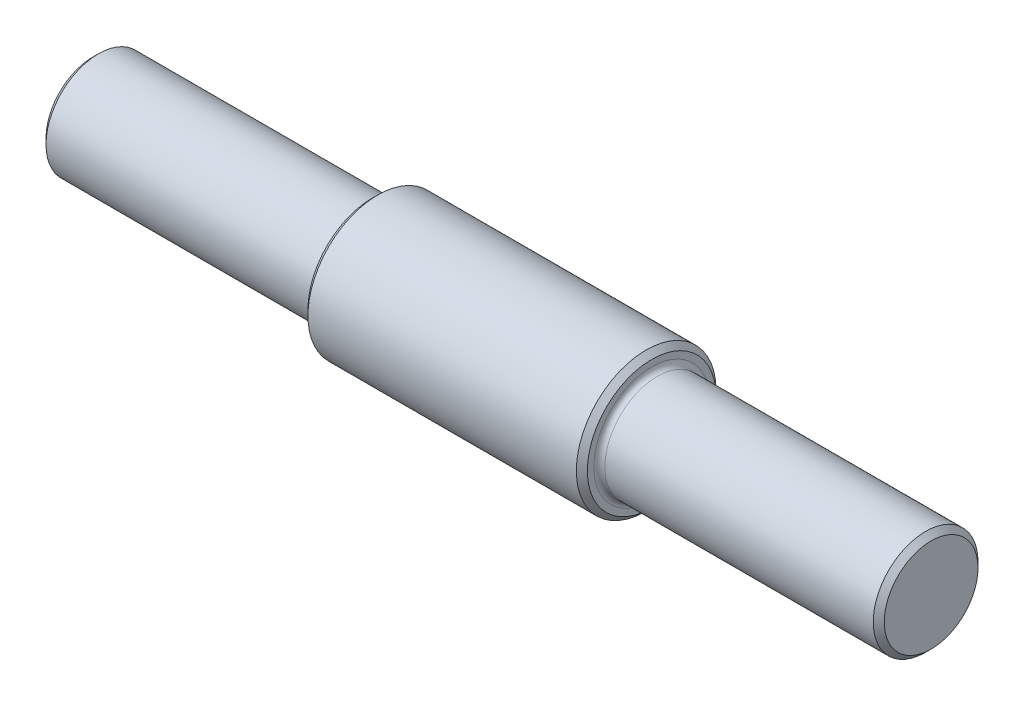
SolidWorks part; units mm, degrees
ref_plane "Alzado" through (0, 0, 0) normal (0, 0, 1) x (1, 0, 0)
ref_plane "Planta" through (0, 0, 0) normal (0, 1, 0) x (1, 0, 0)
ref_plane "Vista lateral" through (0, 0, 0) normal (1, 0, 0) x (0, 0, -1)
sketch "Croquis1" plane through (0, 0, 0) normal (1, 0, 0) x (0, 0, -1)
  circle A0 centre (0, 0) radius 12.7
  dimension "D1" = 25.4
extrude "Saliente-Extruir1" add sketch "Croquis1" along normal mid plane 50.8
sketch "Croquis2" plane through (25.4, 0, 0) normal (1, 0, 0) x (0, 0, -1)
  circle A0 centre (0, 0) radius 9.525
  dimension "D1" = 19.05
extrude "Saliente-Extruir2" add sketch "Croquis2" along normal blind 50.8
fillet "Redondeo1" radius 1 1 edges at (25.4, 0, -9.525)
mirror "Simetría3" about plane through (0, 0, 0) normal (1, 0, 0) of "Saliente-Extruir2"
fillet "Redondeo2" radius 1 1 edges at (-25.4, 0, -9.525)
chamfer "Chaflán1" distance 1 angle 45 2 edges at (-76.2, 0, -9.525) (76.2, 0, -9.525)
chamfer "Chaflán2" distance 1 angle 45 2 edges at (25.4, 0, -12.7) (-25.4, 0, -12.7)
